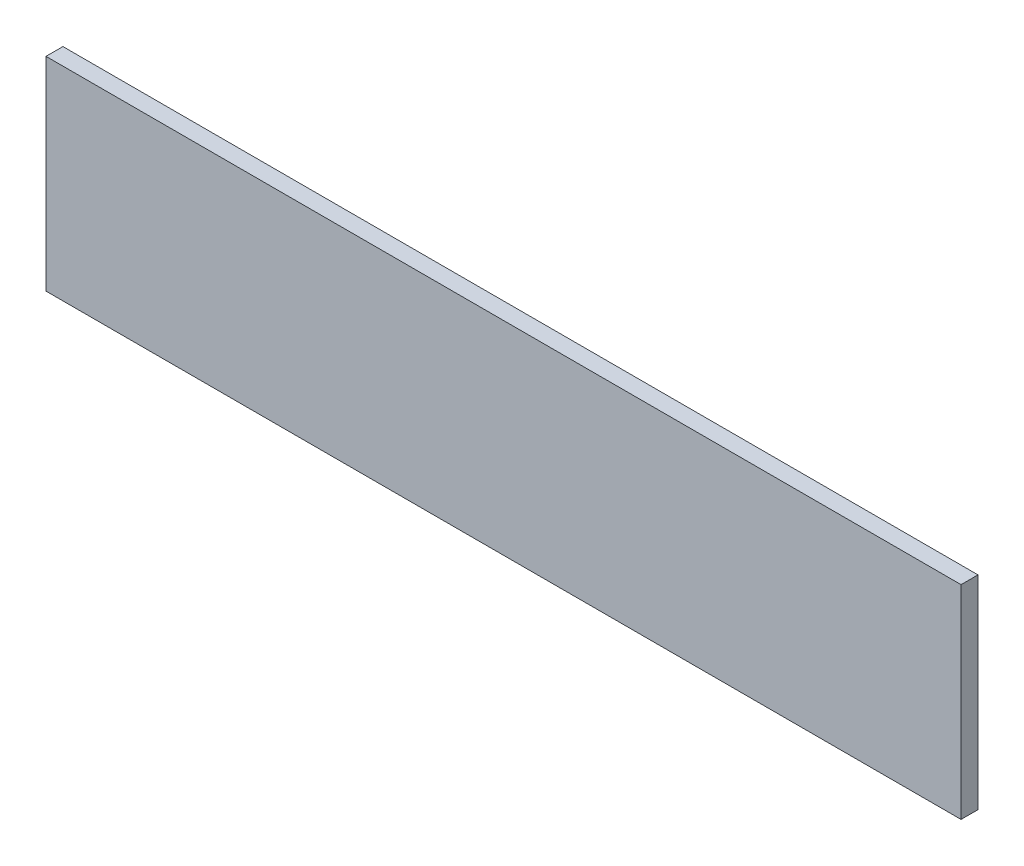
SolidWorks part; units mm, degrees
ref_plane "Front Plane" through (0, 0, 0) normal (0, 0, 1) x (1, 0, 0)
ref_plane "Top Plane" through (0, 0, 0) normal (0, 1, 0) x (1, 0, 0)
ref_plane "Right Plane" through (0, 0, 0) normal (1, 0, 0) x (0, 0, -1)
sketch "Sketch1" plane through (0, 0, 0) normal (0, 0, 1) x (1, 0, 0)
  line L1 (-342.9, 76.2) -> (342.9, 76.2)
  line L2 (-342.9, 76.2) -> (-342.9, -76.2)
  line L3 (-342.9, -76.2) -> (342.9, -76.2)
  line L4 (342.9, 76.2) -> (342.9, -76.2)
  line L5 (-342.9, 76.2) -> (342.9, -76.2) construction
  line L6 (-342.9, -76.2) -> (342.9, 76.2) construction
  point P0 (0, 0)
  dimension "D1" = 685.8
  dimension "D2" = 152.4
extrude "Boss-Extrude1" add sketch "Sketch1" along normal blind 12.7
